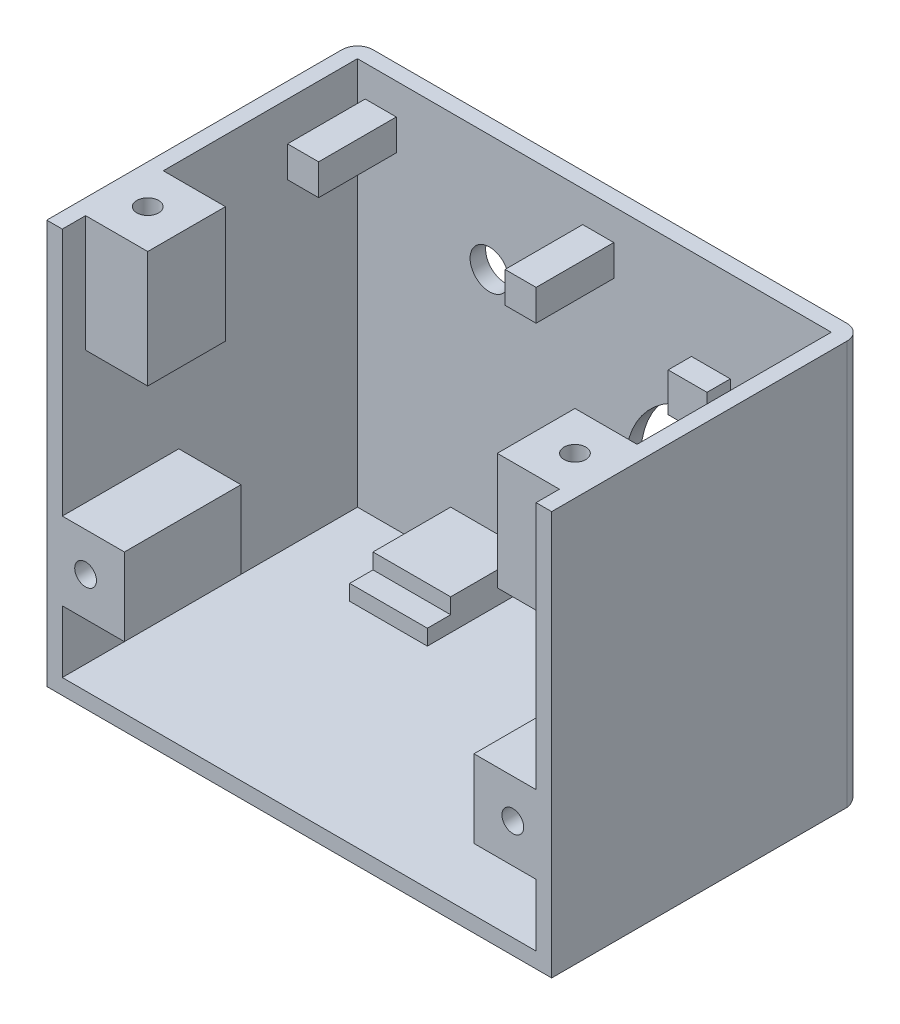
SolidWorks part; units mm, degrees
ref_plane "Front Plane" through (0, 0, 0) normal (0, 0, 1) x (1, 0, 0)
ref_plane "Top Plane" through (0, 0, 0) normal (0, 1, 0) x (1, 0, 0)
ref_plane "Right Plane" through (0, 0, 0) normal (1, 0, 0) x (0, 0, -1)
sketch "Sketch1" plane through (0, 0, 0) normal (0, 0, 1) x (1, 0, 0)
  line L1 (0, 0) -> (65, 0)
  line L2 (0, 0) -> (0, 52)
  line L3 (0, 52) -> (65, 52)
  line L4 (65, 0) -> (65, 52)
  dimension "D1" = 52
  dimension "D2" = 65
extrude "Boss-Extrude1" add sketch "Sketch1" along normal blind 40
shell "Shell1" thickness 2
ref_plane "Plane1" through (32.5, 0, 0) normal (1, 0, 0) x (0, 0, -1)
sketch "Sketch7" plane through (0, 52, 0) normal (0, 1, 0) x (1, 0, 0)
  line L0 (0, -40) -> (0, 0) construction
  line L1 (0, -27) -> (10, -27)
  line L2 (0, -27) -> (0, -37)
  line L3 (0, -37) -> (10, -37)
  line L4 (10, -27) -> (10, -37)
  line L10 (2, -40) -> (0, -40) construction
  dimension "D1" = 3
  dimension "D2" = 10
  dimension "D3" = 10
extrude "Boss-Extrude3" add sketch "Sketch7" against normal blind 15
sketch "Sketch8" plane through (0, 52, 0) normal (0, 1, 0) x (1, 0, 0)
  line L0 (10, -37) -> (10, -27) construction
  line L1 (10, -27) -> (2, -27) construction
  circle A0 centre (5, -32) radius 1.4
  dimension "D1" = 5
  dimension "D2" = 5
extrude "Cut-Extrude3" cut sketch "Sketch8" against normal blind 10
mirror "Mirror3" about plane through (32.5, 0, 0) normal (1, 0, 0) of "Cut-Extrude3", "Boss-Extrude3"
sketch "Sketch10" plane through (0, 0, 40) normal (0, 0, 1) x (1, 0, 0)
  line L0 (0, 52) -> (0, 0) construction
  line L1 (0, 20) -> (10, 20)
  line L2 (0, 20) -> (0, 10)
  line L3 (0, 10) -> (10, 10)
  line L4 (10, 20) -> (10, 10)
  line L5 (0, 0) -> (65, 0) construction
  dimension "D1" = 10
  dimension "D2" = 10
  dimension "D3" = 10
extrude "Boss-Extrude4" add sketch "Sketch10" against normal blind 15
sketch "Sketch11" plane through (0, 0, 40) normal (0, 0, 1) x (1, 0, 0)
  line L0 (10, 10) -> (10, 20) construction
  line L2 (10, 20) -> (2, 20) construction
  circle A0 centre (5, 15) radius 1.4
  dimension "D1" = 5
  dimension "D2" = 5
extrude "Cut-Extrude4" cut sketch "Sketch11" against normal blind 10
mirror "Mirror4" about plane through (32.5, 0, 0) normal (1, 0, 0) of "Boss-Extrude4", "Cut-Extrude4"
sketch "Sketch12" plane through (0, 0, 0) normal (0, 0, -1) x (-1, 0, 0)
  line L0 (0, 52) -> (0, 0) construction
  line L1 (-33, 46) -> (-5, 46)
  line L2 (-33, 46) -> (-33, 6)
  line L3 (-33, 6) -> (-5, 6)
  line L4 (-5, 46) -> (-5, 6)
  line L5 (0, 0) -> (-65, 0) construction
  line L6 (-65, 0) -> (-65, 52) construction
  line L7 (-60, 40.3) -> (-35, 40.3)
  line L8 (-60, 40.3) -> (-60, 7.7)
  line L9 (-60, 7.7) -> (-35, 7.7)
  line L10 (-35, 40.3) -> (-35, 7.7)
  dimension "D1" = 28
  dimension "D2" = 40
  dimension "D3" = 5
  dimension "D4" = 6
  dimension "D5" = 5
  dimension "D6" = 25
  dimension "D7" = 32.6
  dimension "D8" = 7.7
sketch "Sketch13" plane through (0, 0, 0) normal (0, 0, -1) x (-1, 0, 0)
  line L0 (-33, 46) -> (-5, 46) construction
  line L1 (-5, 46) -> (-5, 6) construction
  circle A0 centre (-19, 37) radius 2.5
  dimension "D1" = 9
  dimension "D2" = 14
extrude "Cut-Extrude5" cut sketch "Sketch13" against normal blind 2
sketch "Sketch16" plane through (0, 0, 2) normal (0, 0, 1) x (1, 0, 0)
  line L0 (33, 6) -> (5, 6) construction
  line L1 (14, 8) -> (24, 8)
  line L2 (14, 8) -> (14, 4)
  line L3 (14, 4) -> (24, 4)
  line L4 (24, 8) -> (24, 4)
  line L5 (33, 46) -> (33, 6) construction
  dimension "D1" = 4
  dimension "D2" = 10
  dimension "D3" = 2
  dimension "D4" = 9
extrude "Boss-Extrude5" add sketch "Sketch16" along normal blind 13
sketch "Sketch17" plane through (0, 0, 15) normal (0, 0, 1) x (1, 0, 0)
  line L0 (24, 4) -> (24, 8) construction
  line L1 (14, 8) -> (24, 8)
  line L2 (14, 8) -> (14, 6)
  line L3 (14, 6) -> (24, 6)
  line L4 (24, 8) -> (24, 6)
extrude "Cut-Extrude6" cut sketch "Sketch17" against normal blind 3
sketch "Sketch18" plane through (0, 0, 2) normal (0, 0, 1) x (1, 0, 0)
  line L0 (33, 46) -> (33, 6) construction
  line L1 (31, 48) -> (35, 48)
  line L2 (31, 48) -> (31, 44)
  line L3 (31, 44) -> (35, 44)
  line L4 (35, 48) -> (35, 44)
  line L5 (33, 46) -> (5, 46) construction
  dimension "D1" = 4
  dimension "D2" = 4
  dimension "D3" = 2
  dimension "D4" = 2
extrude "Boss-Extrude6" add sketch "Sketch18" along normal blind 10
sketch "Sketch20" plane through (0, 0, 2) normal (0, 0, 1) x (1, 0, 0)
  line L0 (5, 46) -> (5, 6) construction
  line L1 (3, 48) -> (7, 48)
  line L2 (3, 48) -> (3, 44)
  line L3 (3, 44) -> (7, 44)
  line L4 (7, 48) -> (7, 44)
  line L5 (33, 46) -> (5, 46) construction
  dimension "D1" = 4
  dimension "D2" = 4
  dimension "D3" = 2
  dimension "D4" = 2
extrude "Boss-Extrude7" add sketch "Sketch20" along normal blind 10
fillet "Fillet1" radius 2 3 edges at (32.5, 0, 0) (65, 26, 0) (0, 26, 0)
sketch "Sketch22" plane through (0, 0, 2) normal (0, 0, 1) x (1, 0, 0)
  line L0 (60, 40.3) -> (35, 40.3) construction
  line L1 (45, 40.3) -> (50, 40.3)
  line L2 (45, 40.3) -> (45, 35.3)
  line L3 (45, 35.3) -> (50, 35.3)
  line L4 (50, 40.3) -> (50, 35.3)
  line L5 (35, 40.3) -> (35, 7.7) construction
  dimension "D1" = 5
  dimension "D2" = 5
  dimension "D3" = 10
extrude "Boss-Extrude8" add sketch "Sketch22" along normal blind 3
sketch "Sketch23" plane through (0, 0, 2) normal (0, 0, 1) x (1, 0, 0)
  line L0 (60, 7.7) -> (35, 7.7) construction
  line L1 (45, 7.7) -> (50, 7.7)
  line L2 (45, 7.7) -> (45, 12.7)
  line L3 (45, 12.7) -> (50, 12.7)
  line L4 (50, 7.7) -> (50, 12.7)
  line L5 (35, 40.3) -> (35, 7.7) construction
  dimension "D1" = 5
  dimension "D2" = 5
  dimension "D3" = 10
extrude "Boss-Extrude9" add sketch "Sketch23" along normal blind 3
sketch "Sketch24" plane through (0, 0, 2) normal (0, 0, 1) x (1, 0, 0)
  line L0 (60, 7.7) -> (35, 7.7) construction
  line L2 (35, 40.3) -> (35, 7.7) construction
  circle A0 centre (47.5, 24.03) radius 11
  dimension "D1" = 16.33
  dimension "D2" = 12.5
extrude "Cut-Extrude7" cut sketch "Sketch24" against normal blind 2
